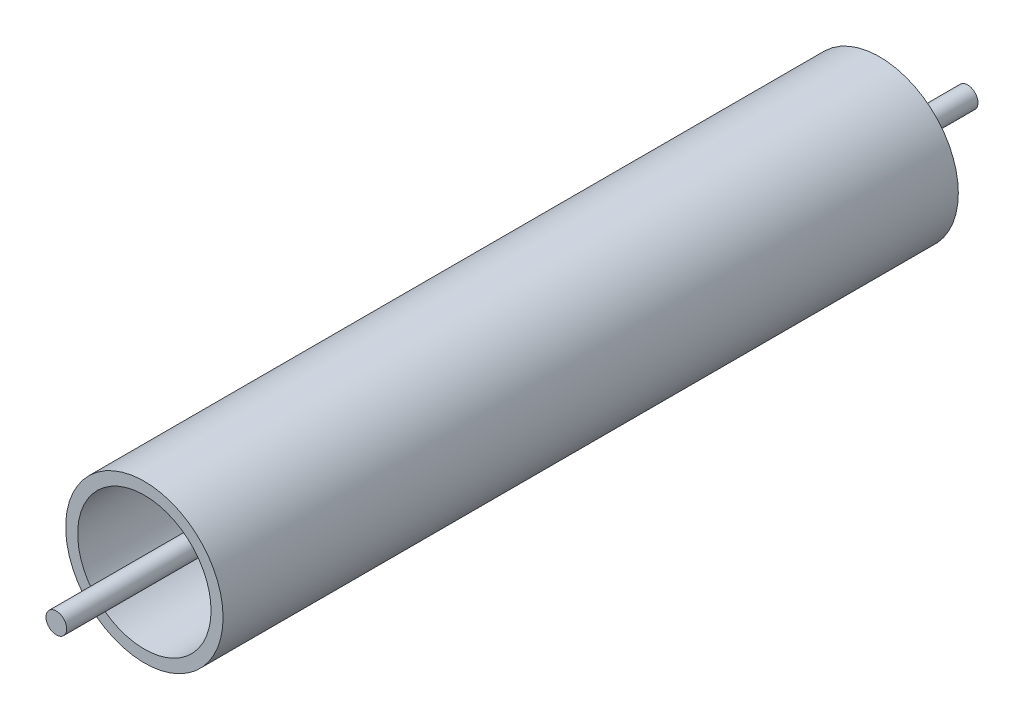
SolidWorks part; units mm, degrees
ref_plane "Front Plane" through (0, 0, 0) normal (0, 0, 1) x (1, 0, 0)
ref_plane "Top Plane" through (0, 0, 0) normal (0, 1, 0) x (1, 0, 0)
ref_plane "Right Plane" through (0, 0, 0) normal (1, 0, 0) x (0, 0, -1)
sketch "Sketch1" plane through (0, 0, 0) normal (0, 0, 1) x (1, 0, 0)
  circle A0 centre (0, 0) radius 3.175
extrude "Boss-Extrude1" add sketch "Sketch1" along normal mid plane 279.4 contours A0
sketch "Sketch2" plane through (0, 0, 0) normal (0, 0, 1) x (1, 0, 0)
  circle A0 centre (0, 0) radius 20.447
  circle A1 centre (0, 0) radius 24.13
  dimension "D1" = 40.894
  dimension "D2" = 48.26
extrude "Boss-Extrude2" add sketch "Sketch2" along normal mid plane 225.425
